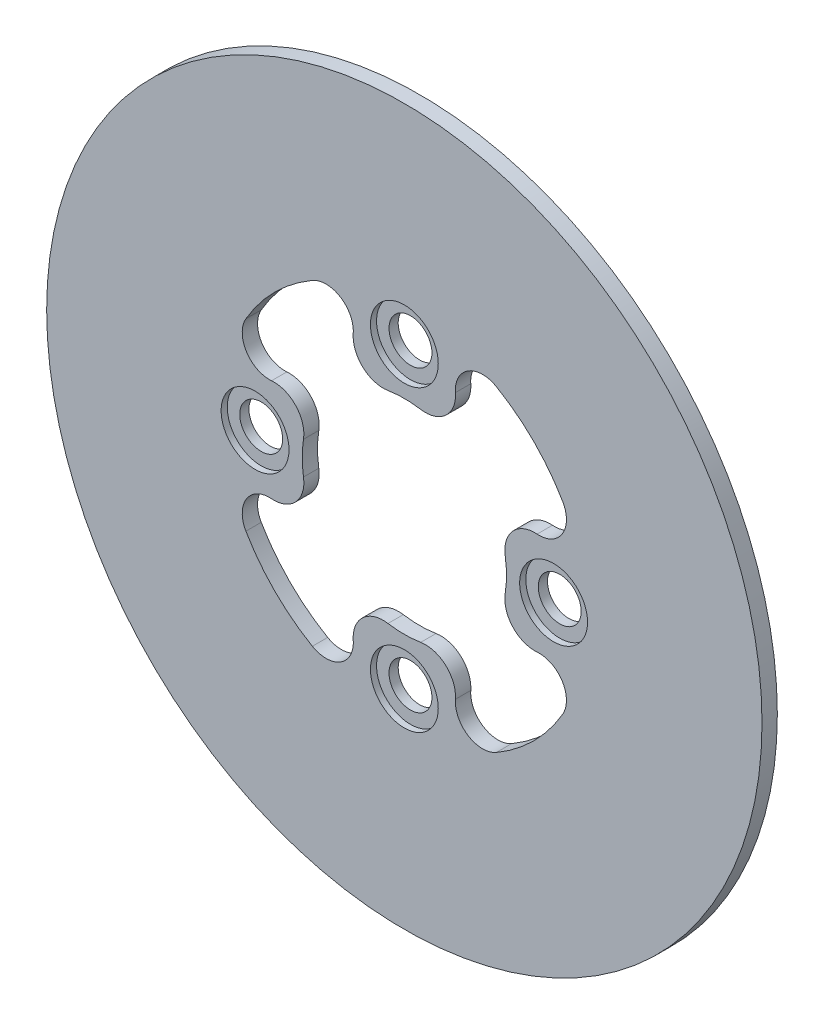
SolidWorks part; units mm, degrees
ref_plane "Alzado" through (0, 0, 0) normal (0, 0, 1) x (1, 0, 0)
ref_plane "Planta" through (0, 0, 0) normal (0, 1, 0) x (1, 0, 0)
ref_plane "Vista lateral" through (0, 0, 0) normal (1, 0, 0) x (0, 0, -1)
sketch "Croquis1" plane through (0, 0, 0) normal (0, 0, 1) x (1, 0, 0)
  line L0 (0, 44.815) -> (0, -25) construction
  line L1 (-25, 0) -> (44.815, 0) construction
  circle A0 centre (0, 0) radius 87.5
  arc A1 (-22.5, 38.7574) -> (-38.7574, 22.5) centre (0, 0) ccw
  arc A2 (-24.6779, 4) -> (-24.6779, -4) centre (0, 0) ccw
  arc A3 (-4, 24.6779) -> (-12.5, 32.4844) centre (-5.1753, 31.929) cw
  arc A4 (-12.5, 32.4844) -> (-22.5, 38.7574) centre (-19.1511, 32.9888) ccw
  arc A5 (12.5, 32.4844) -> (22.5, 38.7574) centre (19.1511, 32.9888) cw
  arc A6 (4, 24.6779) -> (12.5, 32.4844) centre (5.1753, 31.929) ccw
  arc A7 (-22.5, 38.7574) -> (-38.7574, 22.5) centre (0, 0) ccw
  arc A8 (24.6779, 4) -> (32.4844, 12.5) centre (31.929, 5.1753) cw
  arc A9 (32.4844, 12.5) -> (38.7574, 22.5) centre (32.9888, 19.1511) ccw
  arc A10 (24.6779, -4) -> (32.4844, -12.5) centre (31.929, -5.1753) ccw
  arc A11 (32.4844, -12.5) -> (38.7574, -22.5) centre (32.9888, -19.1511) cw
  arc A12 (-22.5, 38.7574) -> (-38.7574, 22.5) centre (0, 0) ccw
  arc A13 (4, -24.6779) -> (12.5, -32.4844) centre (5.1753, -31.929) cw
  arc A14 (12.5, -32.4844) -> (22.5, -38.7574) centre (19.1511, -32.9888) ccw
  arc A15 (-4, -24.6779) -> (-12.5, -32.4844) centre (-5.1753, -31.929) ccw
  arc A16 (-12.5, -32.4844) -> (-22.5, -38.7574) centre (-19.1511, -32.9888) cw
  arc A17 (-22.5, 38.7574) -> (-38.7574, 22.5) centre (0, 0) ccw
  arc A18 (-24.6779, -4) -> (-32.4844, -12.5) centre (-31.929, -5.1753) cw
  arc A19 (-32.4844, -12.5) -> (-38.7574, -22.5) centre (-32.9888, -19.1511) ccw
  arc A20 (-24.6779, 4) -> (-32.4844, 12.5) centre (-31.929, 5.1753) ccw
  arc A21 (-32.4844, 12.5) -> (-38.7574, 22.5) centre (-32.9888, 19.1511) cw
  arc A22 (4, 24.6779) -> (-4, 24.6779) centre (0, 0) ccw
  arc A23 (24.6779, -4) -> (24.6779, 4) centre (0, 0) ccw
  arc A24 (-4, -24.6779) -> (4, -24.6779) centre (0, 0) ccw
  arc A25 (38.7574, 22.5) -> (22.5, 38.7574) centre (0, 0) ccw
  arc A26 (38.7574, 22.5) -> (22.5, 38.7574) centre (0, 0) ccw
  arc A27 (38.7574, 22.5) -> (22.5, 38.7574) centre (0, 0) ccw
  arc A28 (38.7574, 22.5) -> (22.5, 38.7574) centre (0, 0) ccw
  arc A29 (22.5, -38.7574) -> (38.7574, -22.5) centre (0, 0) ccw
  arc A30 (22.5, -38.7574) -> (38.7574, -22.5) centre (0, 0) ccw
  arc A31 (22.5, -38.7574) -> (38.7574, -22.5) centre (0, 0) ccw
  arc A32 (22.5, -38.7574) -> (38.7574, -22.5) centre (0, 0) ccw
  arc A33 (-38.7574, -22.5) -> (-22.5, -38.7574) centre (0, 0) ccw
  arc A34 (-38.7574, -22.5) -> (-22.5, -38.7574) centre (0, 0) ccw
  arc A35 (-38.7574, -22.5) -> (-22.5, -38.7574) centre (0, 0) ccw
  arc A36 (-38.7574, -22.5) -> (-22.5, -38.7574) centre (0, 0) ccw
  point P55 (0, 0)
  dimension "D1" = 175
  dimension "D2" = 89.63
  dimension "D3" = 50
  dimension "D4" = 45
  dimension "D5" = 25
  dimension "D6" = 8
  dimension "D7" = 4
extrude "Saliente-Extruir1" add sketch "Croquis1" along normal blind 3.75 contours A0 A33 A19 A18 A2 A20 A21 A1 A4 A3 A22 A6 A5 A25 A9 A8 A23 A10 A11 A29 A14 A13 A24 A15 A16
sketch "Croquis2" plane through (0, 0, 3.75) normal (0, 0, 1) x (1, 0, 0)
  line L0 (0, 36.515) -> (0, -36.515) construction
  line L1 (-36.515, 0) -> (36.515, 0) construction
  circle A0 centre (-36.515, 0) radius 8.3
  circle A1 centre (0, 36.515) radius 8.3
  circle A2 centre (36.515, 0) radius 8.3
  circle A3 centre (0, -36.515) radius 8.3
  arc A4 (38.7574, 22.5) -> (22.5, 38.7574) centre (0, 0) ccw construction
  arc A5 (22.5, -38.7574) -> (38.7574, -22.5) centre (0, 0) ccw construction
  point P5 (0, 0)
  point P6 (0, 0)
  dimension "D1" = 16.6
extrude "Cortar-Extruir1" cut sketch "Croquis2" against normal blind 1.5
sketch "Croquis3" plane through (0, 0, 3.75) normal (0, 0, 1) x (1, 0, 0)
  circle A0 centre (0, -36.515) radius 8.3 construction
  circle A1 centre (-36.515, 0) radius 8.3 construction
  circle A2 centre (36.515, 0) radius 8.3 construction
  circle A3 centre (0, 36.515) radius 8.3 construction
  circle A4 centre (0, -36.515) radius 8.3 construction
  circle A5 centre (-36.515, 0) radius 8.3 construction
  circle A6 centre (36.515, 0) radius 8.3 construction
  circle A7 centre (0, 36.515) radius 8.3 construction
  circle A8 centre (0, 36.515) radius 5.25
  dimension "D1" = 10.5
extrude "Cortar-Extruir2" cut sketch "Croquis3" against normal through all
pattern_circular "MatrizC1" count 8 over 360 about axis through (0, 0, 3.75) along (0, 0, 1) of "Cortar-Extruir2"
sketch "Croquis4" plane through (0, 0, 3.75) normal (0, 0, 1) x (1, 0, 0)
  circle A0 centre (0, 0) radius 87.5 construction
  point P0 (0, 87.5)
  point P1 (0, 52.5)
  dimension "D1" = 35
